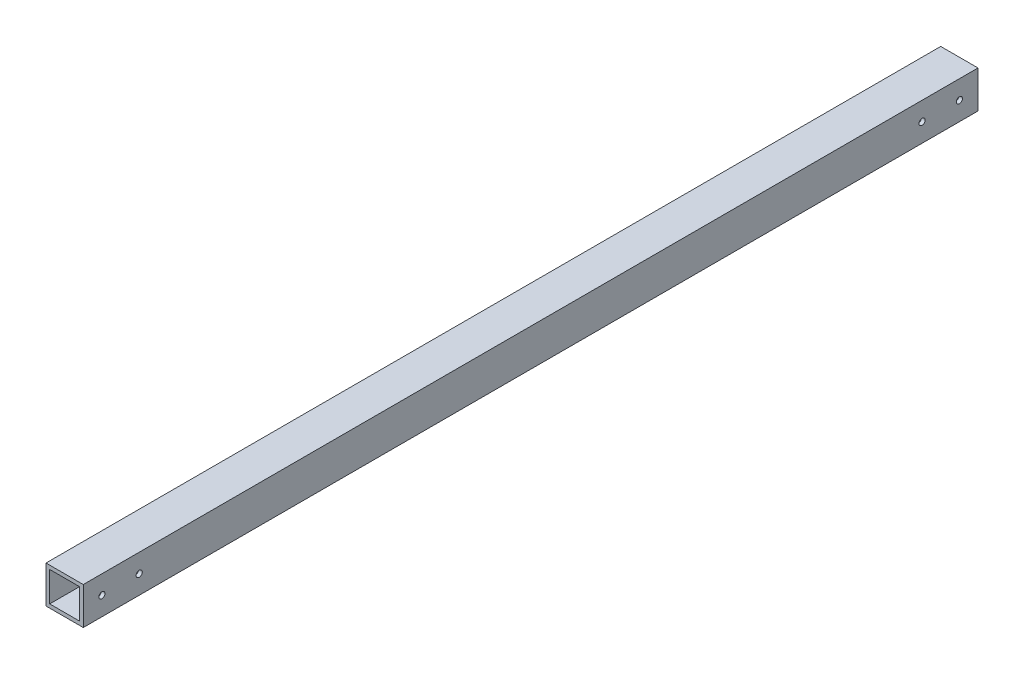
SolidWorks part; units mm, degrees
ref_plane "正面" through (0, 0, 0) normal (0, 0, 1) x (1, 0, 0)
ref_plane "平面" through (0, 0, 0) normal (0, 1, 0) x (1, 0, 0)
ref_plane "右側面" through (0, 0, 0) normal (1, 0, 0) x (0, 0, -1)
sketch "ｽｹｯﾁ1" plane through (0, 0, 0) normal (0, 0, 1) x (1, 0, 0)
  line L1 (-10, 10) -> (10, 10)
  line L2 (-10, 10) -> (-10, -10)
  line L3 (-10, -10) -> (10, -10)
  line L4 (10, 10) -> (10, -10)
  line L5 (-10, 10) -> (10, -10) construction
  line L6 (-10, -10) -> (10, 10) construction
  line L7 (-8, 8) -> (8, 8)
  line L8 (-8, 8) -> (-8, -8)
  line L9 (-8, -8) -> (8, -8)
  line L10 (8, 8) -> (8, -8)
  line L11 (-8, 8) -> (8, -8) construction
  line L12 (-8, -8) -> (8, 8) construction
  point P0 (0, 0)
  point P6 (0, 0)
  dimension "D1" = 20
  dimension "D2" = 20
  dimension "D3" = 16
  dimension "D4" = 16
extrude "ﾎﾞｽ - 押し出し1" add sketch "ｽｹｯﾁ1" along normal blind 560
sketch "ｽｹｯﾁ3" plane through (10, 0, 0) normal (1, 0, 0) x (0, 0, -1)
  line L0 (-560, 0) -> (-530, 0)
  line L1 (-560, -10) -> (-560, 10) construction
  line L2 (-530, 0) -> (-30, 0)
  circle A0 centre (-530, 0) radius 2.2
  circle A1 centre (-30, 0) radius 2.2
  dimension "D2" = 4.4
  dimension "D4" = 4.4
  dimension "D1" = 30
  dimension "D3" = 500
extrude "ｶｯﾄ - 押し出し2" cut sketch "ｽｹｯﾁ3" against normal blind 560
sketch "ｽｹｯﾁ4" plane through (0, 10, 0) normal (0, 1, 0) x (1, 0, 0)
  line L0 (0, -560) -> (0, -550)
  line L1 (10, -560) -> (-10, -560) construction
  line L2 (0, -550) -> (0, -10)
  circle A0 centre (0, -550) radius 2.2
  circle A1 centre (0, -10) radius 2.2
  dimension "D2" = 4.4
  dimension "D4" = 4.4
  dimension "D1" = 10
  dimension "D3" = 540
extrude "ｶｯﾄ - 押し出し3" cut sketch "ｽｹｯﾁ4" against normal blind 560
sketch "ｽｹｯﾁ5" plane through (0, 0, 0) normal (0, 0, -1) x (-1, 0, 0)
  line L1 (-17.7765, -27.2052) -> (17.7765, -27.2052)
  line L2 (-17.7765, -27.2052) -> (-17.7765, 27.2052)
  line L3 (-17.7765, 27.2052) -> (17.7765, 27.2052)
  line L4 (17.7765, -27.2052) -> (17.7765, 27.2052)
  line L5 (-17.7765, -27.2052) -> (17.7765, 27.2052) construction
  line L6 (-17.7765, 27.2052) -> (17.7765, -27.2052) construction
  point P0 (0, 0)
extrude "ｶｯﾄ - 押し出し4" cut sketch "ｽｹｯﾁ5" against normal blind 40
sketch "ｽｹｯﾁ6" plane through (0, 0, 560) normal (0, 0, 1) x (1, 0, 0)
  line L1 (-16.4693, 18.3609) -> (16.4693, 18.3609)
  line L2 (-16.4693, 18.3609) -> (-16.4693, -18.3609)
  line L3 (-16.4693, -18.3609) -> (16.4693, -18.3609)
  line L4 (16.4693, 18.3609) -> (16.4693, -18.3609)
  line L5 (-16.4693, 18.3609) -> (16.4693, -18.3609) construction
  line L6 (-16.4693, -18.3609) -> (16.4693, 18.3609) construction
  point P0 (0, 0)
extrude "ｶｯﾄ - 押し出し5" cut sketch "ｽｹｯﾁ6" against normal blind 40
sketch "ｽｹｯﾁ7" plane through (0, 10, 0) normal (0, 1, 0) x (1, 0, 0)
  line L0 (0, -520) -> (0, -510)
  line L1 (10, -520) -> (-10, -520) construction
  line L2 (0, -510) -> (0, -490)
  circle A0 centre (0, -510) radius 2.1
  circle A1 centre (0, -490) radius 2.1
  dimension "D3" = 4.2
  dimension "D4" = 4.2
  dimension "D1" = 10
  dimension "D2" = 20
sketch "ｽｹｯﾁ8" plane through (10, 0, 0) normal (1, 0, 0) x (0, 0, -1)
  line L0 (-520, 0) -> (-510, 0)
  line L1 (-520, -10) -> (-520, 10) construction
  line L2 (-510, 0) -> (-490, 0)
  line L3 (-40, 0) -> (-50, 0)
  line L4 (-40, -10) -> (-40, 10) construction
  line L5 (-50, 0) -> (-70, 0)
  circle A0 centre (-50, 0) radius 1
  circle A1 centre (-70, 0) radius 1
  circle A2 centre (-490, 0) radius 1
  circle A3 centre (-510, 0) radius 1
  dimension "D3" = 2
  dimension "D4" = 2
  dimension "D7" = 2
  dimension "D8" = 2
  dimension "D1" = 10
  dimension "D2" = 20
  dimension "D5" = 10
  dimension "D6" = 20
extrude "ｶｯﾄ - 押し出し7" cut sketch "ｽｹｯﾁ8" against normal blind 10
sketch "ｽｹｯﾁ9" plane through (0, -10, 0) normal (0, -1, 0) x (1, 0, 0)
  line L0 (0, 520) -> (0, 326)
  line L1 (-10, 520) -> (10, 520) construction
  circle A0 centre (0, 326) radius 2.1
  dimension "D2" = 4.2
  dimension "D1" = 194
sketch "ｽｹｯﾁ10" plane through (0, -10, 0) normal (0, -1, 0) x (1, 0, 0)
  line L0 (0, 40) -> (0, 234)
  line L2 (-10, 40) -> (10, 40) construction
  circle A0 centre (0, 234) radius 2.1
  dimension "D2" = 4.2
  dimension "D1" = 194
sketch "ｽｹｯﾁ11" plane through (0, -10, 0) normal (0, -1, 0) x (1, 0, 0)
  circle A0 centre (0, 234) radius 6
  dimension "D1" = 12
hole_wizard "M4x0.7 ねじ穴1" positions "3Dｽｹｯﾁ1" profile "ｽｹｯﾁ12" tap size "M4x0.7" standard "JIS"
sketch3d "3Dｽｹｯﾁ1"
  line L0 (8, 0, 50) -> (10, 0, 50) construction
  line L1 (8, 0, 70) -> (10, 0, 70) construction
  line L2 (8, 0, 490) -> (10, 0, 490) construction
  line L3 (8, 0, 510) -> (10, 0, 510) construction
  point P0 (10, 0, 50)
  point P4 (10, 0, 70)
  point P8 (10, 0, 490)
  point P12 (10, 0, 510)
sketch "ｽｹｯﾁ12" plane through (10, 0, 50) normal (0, 1, 0) x (0, 0, -1)
  line L0 (0, 0) -> (0, 12.4914)
  line L1 (0, 12.4914) -> (1.65, 11.5)
  line L2 (1.65, 11.5) -> (1.65, 0)
  line L5 (1.65, 0) -> (0, 0)
  line L10 (0, 12.4914) -> (-1.65, 11.5) construction
  line L11 (0, -6.35) -> (0, 107.95) construction
  dimension "ねじ下穴ﾄﾞﾘﾙ直径" = 3.3
  dimension "ねじ下穴ﾄﾞﾘﾙの深さ" = 11.5
  dimension "ﾄﾞﾘﾙ角度" = 118
cosmetic thread "穴のねじ山1" parameters "D1"=2, "D2"=4
cosmetic thread "穴のねじ山2" parameters "D1"=2, "D2"=4
cosmetic thread "穴のねじ山3" parameters "D1"=2, "D2"=4
cosmetic thread "穴のねじ山4" parameters "D1"=2, "D2"=4
